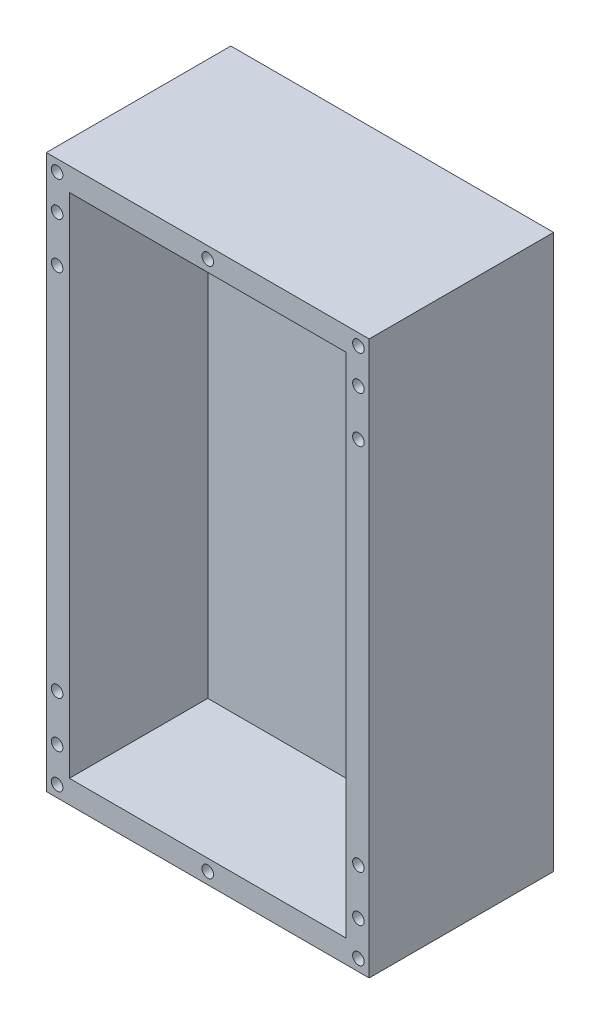
SolidWorks part; units mm, degrees
ref_plane "Front Plane" through (0, 0, 0) normal (0, 0, 1) x (1, 0, 0)
ref_plane "Top Plane" through (0, 0, 0) normal (0, 1, 0) x (1, 0, 0)
ref_plane "Right Plane" through (0, 0, 0) normal (1, 0, 0) x (0, 0, -1)
sketch "Sketch1" plane through (0, 0, 0) normal (0, 0, 1) x (1, 0, 0)
  line L0 (0, 609.6) -> (355.6, 0) construction
  line L1 (0, 609.6) -> (355.6, 609.6)
  line L2 (0, 609.6) -> (0, 0)
  line L3 (0, 0) -> (355.6, 0)
  line L4 (355.6, 609.6) -> (355.6, 0)
  line L5 (355.6, 609.6) -> (0, 0) construction
  line L9 (25.4, 584.2) -> (330.2, 584.2)
  line L10 (25.4, 584.2) -> (25.4, 25.4)
  line L11 (25.4, 25.4) -> (330.2, 25.4)
  line L12 (330.2, 584.2) -> (330.2, 25.4)
  line L13 (25.4, 584.2) -> (330.2, 25.4) construction
  line L14 (330.2, 584.2) -> (25.4, 25.4) construction
  point P12 (177.8, 304.8)
  point P13 (177.8, 304.8)
  dimension "D1" = 355.6
  dimension "D2" = 609.6
  dimension "D3" = 304.8
  dimension "D4" = 558.8
extrude "Boss-Extrude2" add sketch "Sketch1" along normal blind 203.2
ref_plane "Plane4" through (25.4, 584.2, 0) normal (0, -1, 0) x (-1, 0, 0)
sketch "Sketch4" plane through (0, 0, 0) normal (0, 0, -1) x (-1, 0, 0)
  line L1 (-330.2, 584.2) -> (-25.4, 584.2)
  line L2 (-330.2, 584.2) -> (-330.2, 25.4)
  line L3 (-330.2, 25.4) -> (-25.4, 25.4)
  line L4 (-25.4, 584.2) -> (-25.4, 25.4)
extrude "Boss-Extrude3" add sketch "Sketch4" against normal blind 50.8
sketch "Sketch5" plane through (0, 0, 203.2) normal (0, 0, 1) x (1, 0, 0)
  line L0 (177.8, 0) -> (177.8, 609.6) construction
  line L1 (0, 0) -> (355.6, 0) construction
  line L2 (355.6, 609.6) -> (0, 609.6) construction
  line L3 (355.6, 304.8) -> (0, 304.8) construction
  line L4 (355.6, 0) -> (355.6, 609.6) construction
  line L5 (0, 609.6) -> (0, 0) construction
  circle A0 centre (11.8857, 50.9474) radius 6.35
  circle A1 centre (11.8857, 101.7474) radius 6.35
  circle A2 centre (11.8857, 507.8526) radius 6.35
  circle A3 centre (11.8857, 558.6526) radius 6.35
  circle A4 centre (343.7143, 50.9474) radius 6.35
  circle A5 centre (343.7143, 101.7474) radius 6.35
  circle A6 centre (343.7143, 558.6526) radius 6.35
  circle A7 centre (343.7143, 507.8526) radius 6.35
  dimension "D1" = 12.7
  dimension "D2" = 50.8
extrude "Cut-Extrude1" cut sketch "Sketch5" against normal blind 25.4
sketch "Sketch6" plane through (0, 0, 203.2) normal (0, 0, 1) x (1, 0, 0)
  line L0 (0, 304.8) -> (355.6, 304.8) construction
  line L1 (0, 609.6) -> (0, 0) construction
  line L2 (355.6, 0) -> (355.6, 609.6) construction
  circle A0 centre (343.7143, 596.9) radius 6.35
  circle A1 centre (177.8, 596.9) radius 6.35
  circle A2 centre (11.8857, 596.9) radius 6.35
  circle A3 centre (343.7143, 12.7) radius 6.35
  circle A4 centre (177.8, 12.7) radius 6.35
  circle A5 centre (11.8857, 12.7) radius 6.35
extrude "Cut-Extrude2" cut sketch "Sketch6" against normal blind 12.7
sketch "Sketch7" plane through (0, 0, 50.8) normal (0, 0, 1) x (1, 0, 0)
  line L0 (76.0741, 178.8196) -> (278.7408, 178.8196) construction
